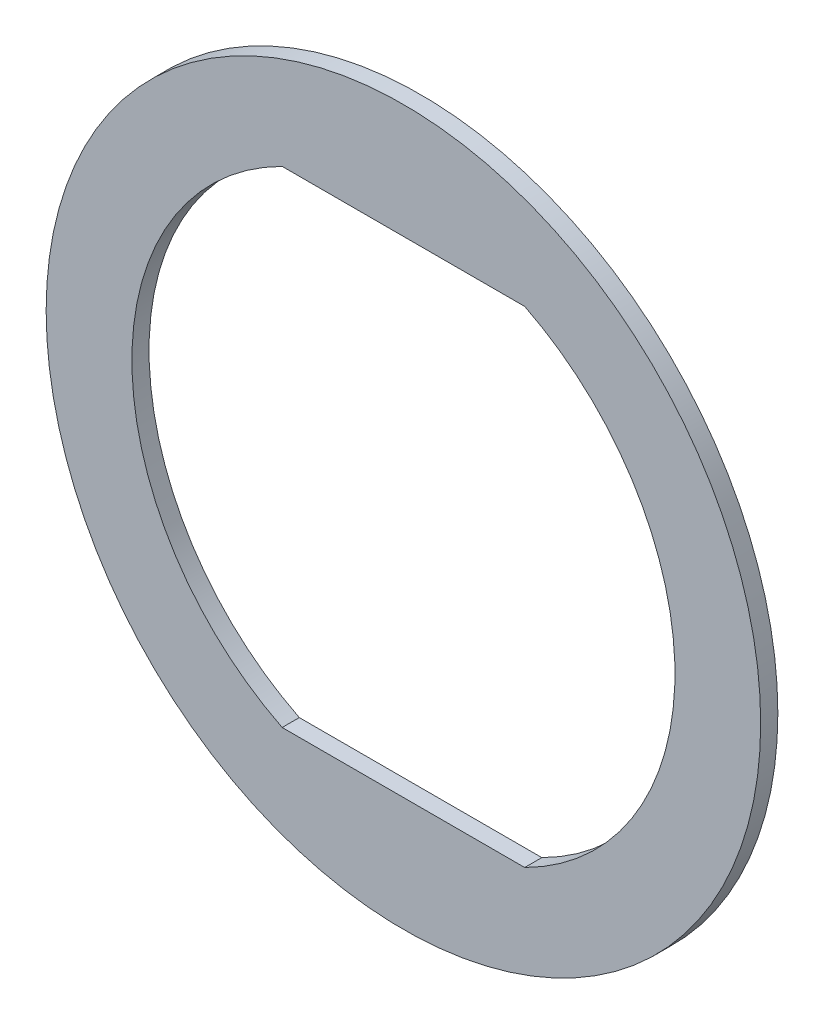
SolidWorks part; units mm, degrees
material "Legierter Stahl"
ref_plane "Ebene vorne" through (0, 0, 0) normal (0, 0, 1) x (1, 0, 0)
ref_plane "Ebene oben" through (0, 0, 0) normal (0, 1, 0) x (1, 0, 0)
ref_plane "Ebene rechts" through (0, 0, 0) normal (1, 0, 0) x (0, 0, -1)
sketch "Skizze1" plane through (0, 0, 0) normal (0, 0, 1) x (1, 0, 0)
  line L0 (-4.2426, 8.5) -> (4.2426, 8.5)
  line L1 (0, 8.5) -> (0, -8.5) construction
  line L2 (4.2426, -8.5) -> (-4.2426, -8.5)
  circle A0 centre (0, 0) radius 12.5
  arc A1 (-4.2426, 8.5) -> (-4.2426, -8.5) centre (0, 0) ccw
  arc A2 (4.2426, -8.5) -> (4.2426, 8.5) centre (0, 0) ccw
  dimension "D2" = 25
  dimension "D3" = 9.5
  dimension "D1" = 17
extrude "Aufsatz-Linear austragen1" add sketch "Skizze1" along normal mid plane 0.6
